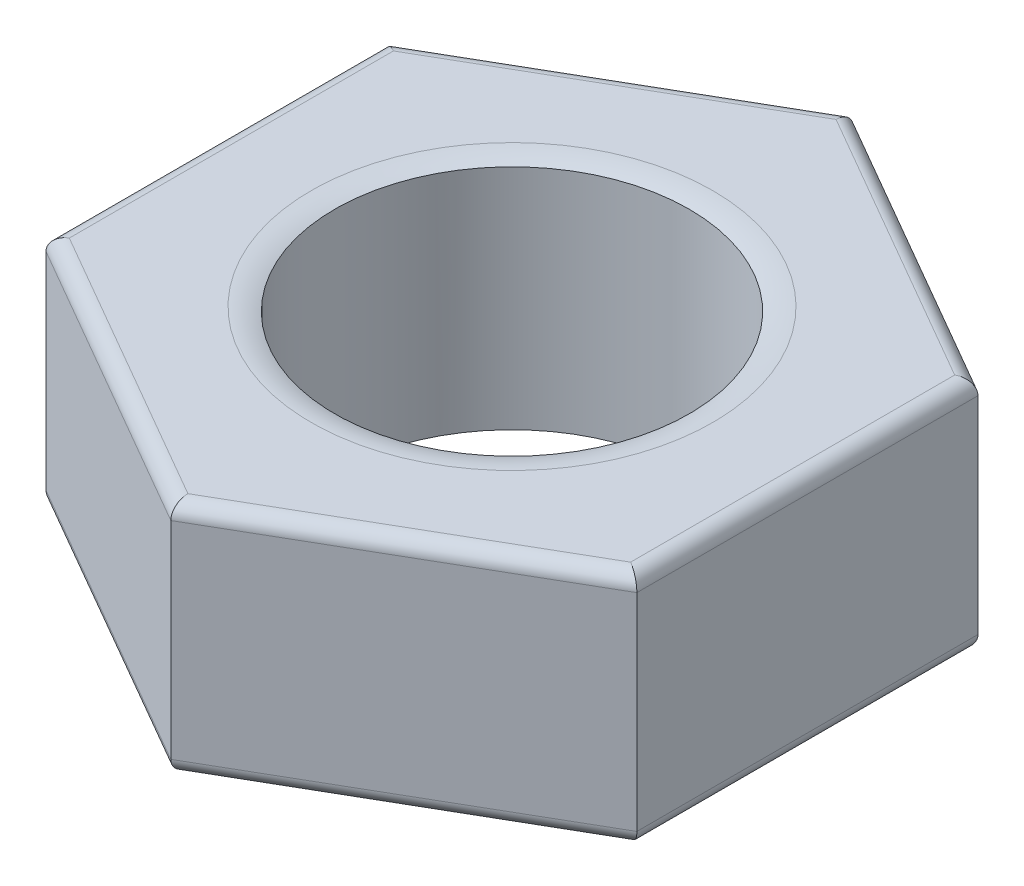
SolidWorks part; units mm, degrees
material "Plain Carbon Steel"
ref_plane "Front Plane" through (0, 0, 0) normal (0, 0, 1) x (1, 0, 0)
ref_plane "Top Plane" through (0, 0, 0) normal (0, 1, 0) x (1, 0, 0)
ref_plane "Right Plane" through (0, 0, 0) normal (1, 0, 0) x (0, 0, -1)
sketch "Sketch1" plane through (0, 0, 0) normal (0, 1, 0) x (1, 0, 0)
  line L1 (0, 2.8868) -> (-2.5, 1.4434)
  line L2 (-2.5, 1.4434) -> (-2.5, -1.4434)
  line L3 (-2.5, -1.4434) -> (0, -2.8868)
  line L4 (0, -2.8868) -> (2.5, -1.4434)
  line L5 (2.5, -1.4434) -> (2.5, 1.4434)
  line L6 (2.5, 1.4434) -> (0, 2.8868)
  circle A0 centre (0, 0) radius 2.5 construction
  circle A1 centre (0, 0) radius 1.5
  dimension "D1" = 5
  dimension "D2" = 3
extrude "Boss-Extrude1" add sketch "Sketch1" along normal blind 2
ref_plane "Plane2" through (0, 2, 0) normal (0, 1, 0) x (1, 0, 0)
ref_plane "Plane3" through (0, 0, 0) normal (0, -1, 0) x (-1, 0, 0)
fillet "Fillet1" radius 0.125 12 edges at (2.5, 0, 0) (1.25, 0, -2.1651) (-1.25, 0, -2.1651) (-2.5, 0, 0) (-1.25, 0, 2.1651) (1.25, 0, 2.1651) (1.25, 2, -2.1651) (2.5, 2, 0) (1.25, 2, 2.1651) (-1.25, 2, 2.1651) (-2.5, 2, 0) (-1.25, 2, -2.1651)
sketch "Sketch3" plane through (0, 2, 0) normal (0, 1, 0) x (1, 0, 0)
  circle A0 centre (0, 0) radius 1.5 construction
  dimension "D1" = 3
sketch "Sketch4" plane through (0, 0, 0) normal (0, -1, 0) x (1, 0, 0)
  circle A0 centre (0, 0) radius 1.5 construction
  circle A1 centre (0, 0) radius 1.5 construction
sketch "Sketch5" plane through (0, 0, 0) normal (1, 0, 0) x (0, 0, -1)
  line L0 (0, 0) -> (0, 2) construction
  line L1 (1.5, 2) -> (-1.5, 2) construction
  line L2 (2.7424, 2) -> (1.3712, 2) construction
  line L3 (1.6995, 2) -> (1.7612, 2)
  line L4 (1.7612, 2) -> (1.7612, 2.1008)
  line L5 (1.7612, 2.1008) -> (1.194, 2.1008)
  line L6 (1.194, 2.1008) -> (1.194, 1.6864)
  line L7 (0, 1) -> (1.8843, 1) construction
  line L8 (1.194, -0.1008) -> (1.194, 0.3136)
  line L9 (1.7612, -0.1008) -> (1.194, -0.1008)
  line L10 (1.7612, 0) -> (1.7612, -0.1008)
  line L11 (1.6995, 0) -> (1.7612, 0)
  arc A0 (1.6995, 2) -> (1.194, 1.6864) centre (1.6995, 1.4358) ccw
  arc A1 (1.6995, 0) -> (1.194, 0.3136) centre (1.6995, 0.5642) cw
revolve "Cut-Revolve1" cut sketch "Sketch5" angle 360 about L0
